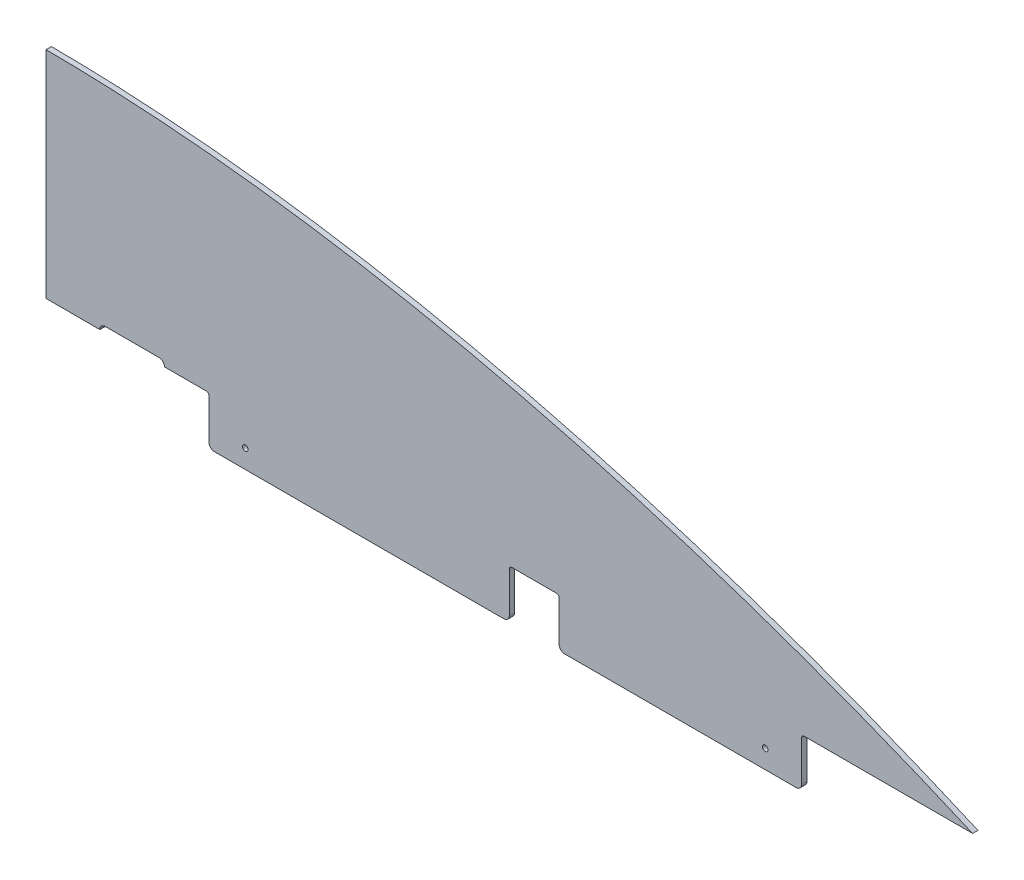
SolidWorks part; units mm, degrees
material "PC High Viscosity"
ref_plane "Front Plane" through (0, 0, 0) normal (0, 0, 1) x (1, 0, 0)
ref_plane "Top Plane" through (0, 0, 0) normal (0, 1, 0) x (1, 0, 0)
ref_plane "Right Plane" through (0, 0, 0) normal (1, 0, 0) x (0, 0, -1)
sketch "Sketch1" plane through (0, 0, 0) normal (0, 0, 1) x (1, 0, 0)
  line L0 (0, 254) -> (0, 0)
  line L1 (0, 0) -> (1092.2, 0)
  spline S0 degree 3 poles (0, 254) (376.5132, 252.2764) (770.2858, 140.4997) (1092.2, 0) knots 0 0 0 0 1 1 1 1
  dimension "D1" = 1092.2
  dimension "D2" = 254
extrude "Boss-Extrude1" add sketch "Sketch1" along normal blind 6.35
sketch "Sketch2" plane through (0, 0, 6.35) normal (0, 0, 1) x (1, 0, 0)
  line L0 (0, 30.48) -> (1020.0945, 30.48) construction
  line L1 (0, 254) -> (0, 0) construction
  line L2 (0, 0) -> (1092.2, 0) construction
  spline S0 degree 3 poles (1092.2, 0) (770.2858, 140.4997) (376.5132, 252.2764) (0, 254) knots 0 0 0 0 1 1 1 1 construction
  point P8 (63.5, 30.48)
  point P9 (977.9, 30.48)
  dimension "D1" = 30.48
  dimension "D2" = 63.5
  dimension "D3" = 914.4
hole_wizard "F (0.257) Diameter Hole1" [suppressed] positions "Sketch3" profile "Sketch4" hole size "F" standard "ANSI Inch"
sketch "Sketch3" plane through (0, 0, 6.35) normal (0, 0, 1) x (1, 0, 0)
  point P0 (63.5, 30.48)
  point P3 (977.9, 30.48)
sketch "Sketch4" plane through (63.5, 30.48, 6.35) normal (1, 0, 0) x (0, -1, 0)
  line L0 (0, 0) -> (0, 6.35)
  line L1 (0, 6.35) -> (3.2639, 6.35)
  line L2 (3.2639, 6.35) -> (3.2639, 0)
  line L5 (3.2639, 0) -> (0, 0)
  line L11 (0, -6.35) -> (0, 107.95) construction
  dimension "Thru Hole Dia." = 6.5278
  dimension "Thru Hole Depth" = 6.35
sketch "Sketch5" plane through (0, 0, 0) normal (0, 0, -1) x (-1, 0, 0)
  line L0 (0, 0) -> (-1092.2, 0) construction
  line L1 (-130.175, 0) -> (-247.65, 0)
  line L2 (-130.175, 0) -> (-130.175, -38.1)
  line L3 (-130.175, -38.1) -> (-247.65, -38.1)
  line L4 (-247.65, 0) -> (-247.65, -38.1)
  line L6 (-815.975, 0) -> (-933.45, 0)
  line L7 (-815.975, 0) -> (-815.975, -38.1)
  line L8 (-815.975, -38.1) -> (-933.45, -38.1)
  line L9 (-933.45, 0) -> (-933.45, -38.1)
  dimension "D1" = 130.175
  dimension "D2" = 568.325
  dimension "D3" = 117.475
  dimension "D4" = 38.1
extrude "Boss-Extrude2" [suppressed] add sketch "Sketch5" against normal up to surface (6.35 mm away)
fillet "Fillet1" [suppressed] radius 3.175
sketch "Sketch6" [suppressed] plane through (0, 0, 0) normal (0, 0, -1) x (-1, 0, 0)
  line L0 (-936.625, 0) -> (-127, 0) construction
  line L1 (-130.175, -6.35) -> (-933.45, -6.35) construction
  line L2 (-130.175, -34.925) -> (-130.175, -3.175) construction
  line L3 (-933.45, -3.175) -> (-933.45, -34.925) construction
  line L4 (-874.7125, -38.1) -> (-874.7125, 0) construction
  line L5 (-930.275, -38.1) -> (-819.15, -38.1) construction
  line L6 (-819.15, -38.1) -> (-244.475, -38.1) construction
  line L7 (-531.8125, -38.1) -> (-531.8125, 0) construction
  line L8 (-188.9125, -38.1) -> (-188.9125, 0) construction
  arc A0 (-933.45, -3.175) -> (-936.625, 0) centre (-936.625, -3.175) ccw construction
  circle A1 centre (-908.05, -9.7282) radius 3.3782
  circle A2 centre (-908.05, 3.3782) radius 3.3782
  circle A3 centre (-841.375, 3.3782) radius 3.3782
  circle A4 centre (-841.375, -9.7282) radius 3.3782
  circle A5 centre (-222.25, -9.7282) radius 3.3782
  circle A6 centre (-222.25, 3.3782) radius 3.3782
  circle A7 centre (-155.575, 3.3782) radius 3.3782
  circle A8 centre (-155.575, -9.7282) radius 3.3782
  dimension "D2" = 6.7564
  dimension "D1" = 6.35
  dimension "D3" = 25.4
extrude "Cut-Extrude1" [suppressed] cut sketch "Sketch6" against normal through all
sketch "Sketch7" plane through (0, 0, 0) normal (0, 0, -1) x (-1, 0, 0)
  line L0 (0, 0) -> (-1092.2, 0) construction
  line L1 (-63.5, 0) -> (-133.35, 0)
  line L3 (-69.85, 6.35) -> (-133.35, 6.35)
  line L4 (0, 0) -> (-1092.2, 0) construction
  arc A0 (-133.35, 6.35) -> (-139.7, 0) centre (-133.35, 0) ccw
  arc A1 (-69.85, 6.35) -> (-63.5, 0) centre (-69.85, 0) cw
  dimension "D1" = 6.35
  dimension "D2" = 63.5
  dimension "D3" = 63.5
extrude "Cut-Extrude2" cut sketch "Sketch7" against normal through all
sketch "Sketch8" plane through (0, 0, 6.35) normal (0, 0, 1) x (1, 0, 0)
  line L0 (139.7, 0) -> (1092.2, 0) construction
  line L1 (192.0875, 0) -> (890.5875, 0)
  line L2 (192.0875, 0) -> (192.0875, -57.15)
  line L3 (192.0875, -57.15) -> (890.5875, -57.15)
  line L4 (890.5875, 0) -> (890.5875, -57.15)
  dimension "D1" = 57.15
  dimension "D2" = 201.6125
  dimension "D3" = 52.3875
extrude "Boss-Extrude3" add sketch "Sketch8" against normal up to surface (6.35 mm away) up to face at (292.1, 20.3329, 0)
sketch "Sketch12" plane through (0, 0, 6.35) normal (0, 0, 1) x (1, 0, 0)
  line L0 (192.0875, -57.15) -> (890.5875, -57.15) construction
  line L1 (604.8375, -57.15) -> (546.1, -57.15)
  line L2 (604.8375, -57.15) -> (604.8375, 0)
  line L3 (604.8375, 0) -> (546.1, 0)
  line L4 (546.1, -57.15) -> (546.1, 0)
  line L5 (890.5875, -57.15) -> (890.5875, 0) construction
  line L6 (0, 254) -> (0, 0) construction
  line L7 (139.7, 0) -> (192.0875, 0) construction
  dimension "D1" = 285.75
  dimension "D2" = 546.1
extrude "Cut-Extrude3" cut sketch "Sketch12" against normal through all
fillet "Fillet2" radius 3.175 4 edges at (890.5875, 0, 3.175) (192.0875, 0, 3.175) (546.1, 0, 3.175) (604.8375, 0, 3.175)
fillet "Fillet3" radius 6.35 4 edges at (192.0875, -57.15, 3.175) (890.5875, -57.15, 3.175) (546.1, -57.15, 3.175) (604.8375, -57.15, 3.175)
sketch "Sketch9" plane through (0, 0, 0) normal (0, 0, -1) x (-1, 0, 0)
  line L4 (-192.0875, -50.8) -> (-192.0875, -3.175) construction
  line L5 (-884.2375, -57.15) -> (-611.1875, -57.15) construction
  line L6 (-890.5875, -3.175) -> (-890.5875, -50.8) construction
  point P0 (-234.95, -35.306)
  point P2 (-847.725, -35.306)
  dimension "D1" = 42.8625
  dimension "D2" = 21.844
  dimension "D3" = 42.8625
hole_wizard "F (0.257) Diameter Hole2" positions "Sketch10" profile "Sketch11" hole size "F" standard "ANSI Inch" end condition through all
sketch "Sketch10" plane through (0, 0, 0) normal (0, 0, -1) x (-1, 0, 0)
  point P0 (-847.725, -35.306)
  point P3 (-234.95, -35.306)
sketch "Sketch11" plane through (847.725, -35.306, 0) normal (1, 0, 0) x (0, 1, 0)
  line L0 (0, 0) -> (0, 6.35)
  line L1 (0, 6.35) -> (3.2639, 6.35)
  line L2 (3.2639, 6.35) -> (3.2639, 0)
  line L5 (3.2639, 0) -> (0, 0)
  line L11 (0, -6.35) -> (0, 107.95) construction
  dimension "Thru Hole Dia." = 6.5278
  dimension "Thru Hole Depth" = 6.35
equation "\"D3@Sketch9\"=\"D1@Sketch9\""
